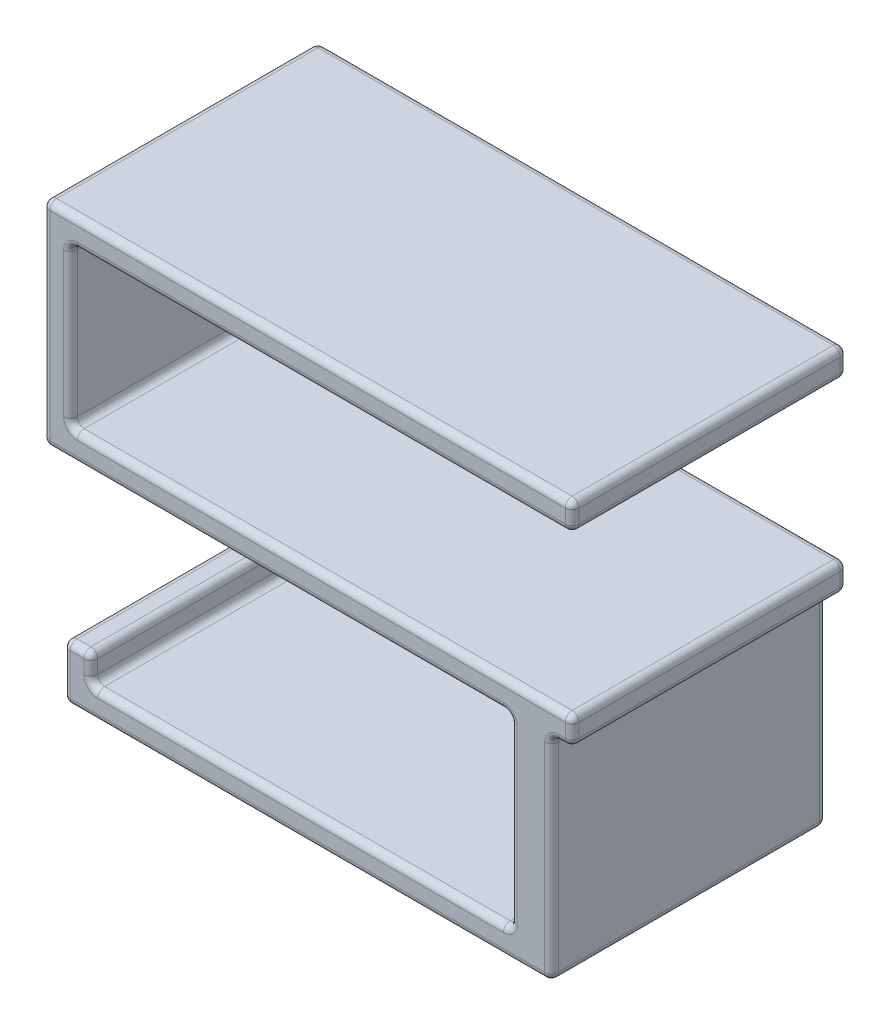
SolidWorks part; units mm, degrees
ref_plane "Plano frontal" through (0, 0, 0) normal (0, 0, 1) x (1, 0, 0)
ref_plane "Plano superior" through (0, 0, 0) normal (0, 1, 0) x (1, 0, 0)
ref_plane "Plano direito" through (0, 0, 0) normal (1, 0, 0) x (0, 0, -1)
sketch "Esboço2" plane through (0, 0, 0) normal (0, 0, 1) x (1, 0, 0)
  line L1 (-48.4735, 6.7694) -> (11.5265, 6.7694)
  line L2 (-48.4735, 6.7694) -> (-48.4735, 3.7694)
  line L3 (-48.4735, 3.7694) -> (11.5265, 3.7694)
  line L4 (11.5265, 6.7694) -> (11.5265, 3.7694)
  dimension "D1" = 3
  dimension "D2" = 60
extrude "Ressalto-extrusão2" add sketch "Esboço2" along normal blind 40
sketch "Esboço3" plane through (0, 6.7694, 0) normal (0, 1, 0) x (1, 0, 0)
  line L0 (11.5265, -40) -> (-48.4735, -40) construction
  line L1 (-46.4735, -40) -> (-62.4735, -40)
  line L2 (-46.4735, -40) -> (-46.4735, 0)
  line L3 (-46.4735, 0) -> (-62.4735, 0)
  line L4 (-62.4735, -40) -> (-62.4735, 0)
  dimension "D1" = 2
  dimension "D2" = 14
  dimension "D3" = 40
other "Alinhar grupo1"
extrude "Ressalto-extrusão3" add sketch "Esboço3" along normal blind 3
sketch "Esboço4" plane through (0, 6.7694, 0) normal (0, -1, 0) x (1, 0, 0)
  line L1 (-62.4735, 40) -> (-64.4735, 40)
  line L2 (-62.4735, 40) -> (-62.4735, 0)
  line L3 (-62.4735, 0) -> (-64.4735, 0)
  line L4 (-64.4735, 40) -> (-64.4735, 0)
  dimension "D1" = 2
  dimension "D2" = 40
extrude "Ressalto-extrusão4" add sketch "Esboço4" against normal blind 3
sketch "Esboço5" plane through (0, 6.7694, 0) normal (0, -1, 0) x (1, 0, 0)
  line L0 (-48.4735, 0) -> (-64.4735, 0) construction
  line L1 (-64.4735, 40) -> (-62.4732, 40)
  line L2 (-64.4735, 40) -> (-64.4735, 0)
  line L3 (-64.4735, 0) -> (-62.4732, 0)
  line L4 (-62.4732, 40) -> (-62.4732, 0)
  dimension "D1" = 2.0003
  dimension "D2" = 40
extrude "Ressalto-extrusão5" add sketch "Esboço5" along normal blind 26
sketch "Esboço6" plane through (0, 0, 40) normal (0, 0, 1) x (1, 0, 0)
  line L1 (-64.4735, -19.2306) -> (-46.4735, -19.2306)
  line L2 (-64.4735, -19.2306) -> (-64.4735, -16.2306)
  line L3 (-64.4735, -16.2306) -> (-46.4735, -16.2306)
  line L4 (-46.4735, -19.2306) -> (-46.4735, -16.2306)
  dimension "D1" = 18
  dimension "D2" = 3
extrude "Ressalto-extrusão6" add sketch "Esboço6" against normal blind 40
sketch "Esboço9" plane through (0, -16.2306, 0) normal (0, 1, 0) x (1, 0, 0)
  line L1 (-46.4735, -40) -> (-49.4735, -40)
  line L2 (-46.4735, -40) -> (-46.4735, 0)
  line L3 (-46.4735, 0) -> (-49.4735, 0)
  line L4 (-49.4735, -40) -> (-49.4735, 0)
  dimension "D1" = 3
  dimension "D2" = 40
extrude "Ressalto-extrusão8" add sketch "Esboço9" along normal blind 3
sketch "Esboço10" plane through (-46.4735, 0, 0) normal (1, 0, 0) x (0, 0, -1)
  line L1 (-40, -13.2306) -> (0, -13.2306)
  line L2 (-40, -13.2306) -> (-40, -16.2306)
  line L3 (-40, -16.2306) -> (0, -16.2306)
  line L4 (0, -13.2306) -> (0, -16.2306)
  dimension "D1" = 3
  dimension "D2" = 40
extrude "Ressalto-extrusão9" add sketch "Esboço10" along normal blind 60
sketch "Esboço11" plane through (0, 0, 40) normal (0, 0, 1) x (1, 0, 0)
  line L2 (-49.4735, -13.2306) -> (-48.4735, -13.2306)
  line L3 (-49.4735, -13.2306) -> (-49.4735, -16.2306)
  line L4 (-49.4735, -16.2306) -> (-48.4735, -16.2306)
  line L5 (-48.4735, -13.2306) -> (-48.4735, -16.2306)
  dimension "D1" = 3
  dimension "D2" = 1
extrude "Corte-extrusão1" cut sketch "Esboço11" against normal up to surface (40 mm away) up to face at (-36.5985, -4.7306, 0)
sketch "Esboço12" plane through (0, 0, 40) normal (0, 0, 1) x (1, 0, 0)
  line L0 (-48.4735, -13.2306) -> (13.5265, -13.2306) construction
  line L1 (13.5265, -16.2306) -> (11.5265, -16.2306)
  line L2 (13.5265, -16.2306) -> (13.5265, -13.2306)
  line L3 (13.5265, -13.2306) -> (11.5265, -13.2306)
  line L4 (11.5265, -16.2306) -> (11.5265, -13.2306)
  dimension "D1" = 3
  dimension "D2" = 2
extrude "Corte-extrusão2" cut sketch "Esboço12" against normal up to surface (40 mm away) up to face at (-36.4735, -4.7306, 0)
sketch "Esboço13" plane through (0, -16.2306, 0) normal (0, -1, 0) x (1, 0, 0)
  line L0 (11.5265, 40) -> (-46.4735, 40) construction
  line L1 (8.5265, 40) -> (5.5265, 40)
  line L2 (8.5265, 40) -> (8.5265, 0)
  line L3 (8.5265, 0) -> (5.5265, 0)
  line L4 (5.5265, 40) -> (5.5265, 0)
  line L5 (11.5265, 0) -> (-46.4735, 0) construction
  dimension "D1" = 3
  dimension "D2" = 3
  dimension "D3" = 40
extrude "Ressalto-extrusão10" add sketch "Esboço13" along normal blind 35
sketch "Esboço14" plane through (5.5265, 0, 0) normal (-1, 0, 0) x (0, 0, 1)
  line L0 (40, -51.2306) -> (40, -16.2306) construction
  line L1 (0, -51.2306) -> (40, -51.2306)
  line L2 (0, -51.2306) -> (0, -48.2306)
  line L3 (0, -48.2306) -> (40, -48.2306)
  line L4 (40, -51.2306) -> (40, -48.2306)
  dimension "D1" = 3
  dimension "D2" = 40
extrude "Ressalto-extrusão11" add sketch "Esboço14" along normal blind 60
sketch "Esboço15" plane through (0, -48.2306, 0) normal (0, 1, 0) x (1, 0, 0)
  line L1 (-54.4735, -40) -> (-52.4735, -40)
  line L2 (-54.4735, -40) -> (-54.4735, 0)
  line L3 (-54.4735, 0) -> (-52.4735, 0)
  line L4 (-52.4735, -40) -> (-52.4735, 0)
  dimension "D1" = 40
  dimension "D2" = 2
extrude "Ressalto-extrusão12" add sketch "Esboço15" along normal blind 3
sketch "Esboço16" plane through (0, -48.2306, 0) normal (0, 1, 0) x (1, 0, 0)
  line L0 (-52.4735, -40) -> (5.5265, -40) construction
  line L1 (2.5265, -40) -> (5.5265, -40)
  line L2 (2.5265, -40) -> (2.5265, 0)
  line L3 (2.5265, 0) -> (5.5265, 0)
  line L4 (5.5265, -40) -> (5.5265, 0)
  dimension "D1" = 55
  dimension "D2" = 3
  dimension "D3" = 40
extrude "Ressalto-extrusão13" add sketch "Esboço16" along normal up to surface (32 mm away) up to face at (-20.4735, -16.2306, 20)
sketch "Esboço17" plane through (-46.4735, 0, 0) normal (1, 0, 0) x (0, 0, -1)
  line L1 (-40, -19.2306) -> (0, -19.2306)
  line L2 (-40, -19.2306) -> (-40, -16.2306)
  line L3 (-40, -16.2306) -> (0, -16.2306)
  line L4 (0, -19.2306) -> (0, -16.2306)
  dimension "D1" = 40
extrude "Ressalto-extrusão14" add sketch "Esboço17" along normal blind 1
sketch "Esboço18" plane through (0, 0, 40) normal (0, 0, 1) x (1, 0, 0)
  line L1 (8.5265, -51.2306) -> (5.5265, -51.2306)
  line L2 (8.5265, -51.2306) -> (8.5265, -16.2306)
  line L3 (8.5265, -16.2306) -> (5.5265, -16.2306)
  line L4 (5.5265, -51.2306) -> (5.5265, -16.2306)
  dimension "D1" = 3
  dimension "D2" = 35
extrude "Corte-extrusão3" cut sketch "Esboço18" against normal up to surface (40 mm away) up to face at (-32.3902, -16.5639, 0)
sketch "Esboço19" plane through (0, 0, 40) normal (0, 0, 1) x (1, 0, 0)
  line L0 (11.5265, 6.7694) -> (-46.4735, 6.7694) construction
  line L1 (-46.4735, 9.7694) -> (-45.4735, 9.7694)
  line L2 (-46.4735, 9.7694) -> (-46.4735, 6.7694)
  line L3 (-46.4735, 6.7694) -> (-45.4735, 6.7694)
  line L4 (-45.4735, 9.7694) -> (-45.4735, 6.7694)
  dimension "D1" = 1
extrude "Ressalto-extrusão15" add sketch "Esboço19" against normal blind 40
sketch "Esboço20" plane through (0, 0, 40) normal (0, 0, 1) x (1, 0, 0)
  line L1 (-52.4735, -48.2306) -> (-51.4735, -48.2306)
  line L2 (-52.4735, -48.2306) -> (-52.4735, -45.2306)
  line L3 (-52.4735, -45.2306) -> (-51.4735, -45.2306)
  line L4 (-51.4735, -48.2306) -> (-51.4735, -45.2306)
  dimension "D1" = 3
  dimension "D2" = 1
extrude "Ressalto-extrusão16" add sketch "Esboço20" against normal blind 40
sketch "Esboço21" plane through (0, 0, 40) normal (0, 0, 1) x (1, 0, 0)
  line L1 (-64.4735, -19.2306) -> (-65.4735, -19.2306)
  line L2 (-64.4735, -19.2306) -> (-64.4735, 9.7694)
  line L3 (-64.4735, 9.7694) -> (-65.4735, 9.7694)
  line L4 (-65.4735, -19.2306) -> (-65.4735, 9.7694)
  dimension "D1" = 1
  dimension "D2" = 29
extrude "Ressalto-extrusão17" add sketch "Esboço21" against normal up to surface (40 mm away) up to face at (-32.4735, -16.5639, 0)
sketch "Esboço22" plane through (0, 0, 40) normal (0, 0, 1) x (1, 0, 0)
  line L2 (-45.4735, -19.2306) -> (11.5265, -19.2306)
  line L3 (-45.4735, -19.2306) -> (-45.4735, -16.2306)
  line L4 (-45.4735, -16.2306) -> (11.5265, -16.2306)
  line L5 (11.5265, -19.2306) -> (11.5265, -16.2306)
extrude "Ressalto-extrusão18" add sketch "Esboço22" against normal up to surface (40 mm away) up to face at (-32.5568, -16.5639, 0)
sketch "Esboço23" plane through (0, 0, 40) normal (0, 0, 1) x (1, 0, 0)
  line L0 (11.5265, -13.2306) -> (11.5265, -19.2306) construction
  line L1 (-48.4735, -13.2306) -> (11.5265, -13.2306)
  line L2 (-48.4735, -13.2306) -> (-48.4735, -16.2306)
  line L3 (-48.4735, -16.2306) -> (11.5265, -16.2306)
  line L4 (11.5265, -13.2306) -> (11.5265, -16.2306)
  dimension "D1" = 3
  dimension "D2" = 60
extrude "Corte-extrusão4" cut sketch "Esboço23" against normal up to surface (40 mm away) up to face at (-31.3826, -16.8669, 0)
sketch "Esboço24" plane through (0, 0, 40) normal (0, 0, 1) x (1, 0, 0)
  line L3 (11.5265, -19.2306) -> (-65.4735, -19.2306)
  line L4 (11.5265, -19.2306) -> (11.5265, -20.2306)
  line L5 (11.5265, -20.2306) -> (-65.4735, -20.2306)
  line L6 (-65.4735, -19.2306) -> (-65.4735, -20.2306)
  dimension "D1" = 77
  dimension "D2" = 1
extrude "Ressalto-extrusão19" add sketch "Esboço24" against normal up to surface (40 mm away) up to face at (-29.6735, -17.2306, 0)
sketch "Esboço25" plane through (0, 0, 40) normal (0, 0, 1) x (1, 0, 0)
  line L1 (11.5265, 6.7694) -> (-65.4735, 6.7694)
  line L2 (11.5265, 6.7694) -> (11.5265, 10.7694)
  line L3 (11.5265, 10.7694) -> (-65.4735, 10.7694)
  line L4 (-65.4735, 6.7694) -> (-65.4735, 10.7694)
  dimension "D1" = 77
  dimension "D2" = 4
extrude "Ressalto-extrusão20" add sketch "Esboço25" against normal up to surface (40 mm away) up to face at (-29.6735, -17.4306, 0)
sketch "Esboço26" plane through (0, 0, 40) normal (0, 0, 1) x (1, 0, 0)
  line L0 (11.5265, 3.7694) -> (11.5265, 10.7694) construction
  line L1 (-48.4735, 3.7694) -> (11.5265, 3.7694)
  line L2 (-48.4735, 3.7694) -> (-48.4735, 6.7694)
  line L3 (-48.4735, 6.7694) -> (11.5265, 6.7694)
  line L4 (11.5265, 3.7694) -> (11.5265, 6.7694)
  dimension "D1" = 3
  dimension "D2" = 60
extrude "Corte-extrusão5" cut sketch "Esboço26" against normal up to surface (40 mm away) up to face at (-27.9179, -20.0084, 0)
sketch "Esboço27" plane through (0, 0, 40) normal (0, 0, 1) x (1, 0, 0)
  line L0 (-62.4732, 6.7694) -> (11.5265, 6.7694) construction
  line L1 (-62.4732, -16.2306) -> (-61.4732, -16.2306)
  line L2 (-62.4732, -16.2306) -> (-62.4732, 6.7694)
  line L3 (-62.4732, 6.7694) -> (-61.4732, 6.7694)
  line L4 (-61.4732, -16.2306) -> (-61.4732, 6.7694)
  dimension "D1" = 1
extrude "Ressalto-extrusão21" add sketch "Esboço27" against normal up to surface (40 mm away) up to face at (-25.3485, -22.9806, 0)
sketch "Esboço28" plane through (0, 0, 40) normal (0, 0, 1) x (1, 0, 0)
  line L0 (5.5265, -20.2306) -> (11.5265, -20.2306) construction
  line L1 (5.5265, -51.2306) -> (8.5265, -51.2306)
  line L2 (5.5265, -51.2306) -> (5.5265, -20.2306)
  line L3 (5.5265, -20.2306) -> (8.5265, -20.2306)
  line L4 (8.5265, -51.2306) -> (8.5265, -20.2306)
  dimension "D1" = 3
extrude "Ressalto-extrusão22" add sketch "Esboço28" against normal up to surface (40 mm away) up to face at (-25.2235, -22.9806, 0)
sketch "Esboço29" plane through (0, 0, 40) normal (0, 0, 1) x (1, 0, 0)
  line L0 (-51.4735, -48.2306) -> (-51.4735, -45.2306) construction
  line L1 (2.5265, -48.2306) -> (-51.4735, -48.2306)
  line L2 (2.5265, -48.2306) -> (2.5265, -47.2306)
  line L3 (2.5265, -47.2306) -> (-51.4735, -47.2306)
  line L4 (-51.4735, -48.2306) -> (-51.4735, -47.2306)
  dimension "D1" = 54
  dimension "D2" = 1
extrude "Ressalto-extrusão24" add sketch "Esboço29" against normal up to surface (40 mm away) up to face at (-24.8485, -22.9806, 0)
sketch "Esboço33" plane through (0, 0, 40) normal (0, 0, 1) x (1, 0, 0)
  line L0 (8.5265, -51.2306) -> (-54.4735, -51.2306) construction
  line L1 (-51.5065, -51.2306) -> (-55.5065, -51.2306)
  line L2 (-51.5065, -51.2306) -> (-51.5065, -43.2306)
  line L3 (-51.5065, -43.2306) -> (-55.5065, -43.2306)
  line L4 (-55.5065, -51.2306) -> (-55.5065, -43.2306)
  dimension "D1" = 4
  dimension "D2" = 8
extrude "Ressalto-extrusão25" add sketch "Esboço33" against normal up to surface (40 mm away) up to face at (-24.8485, -22.8556, 0)
sketch "Esboço35" plane through (0, 0, 40) normal (0, 0, 1) x (1, 0, 0)
  line L1 (-51.4735, -47.2306) -> (-55.5065, -47.2306)
  line L2 (-51.4735, -47.2306) -> (-51.4735, -43.2306)
  line L3 (-51.4735, -43.2306) -> (-55.5065, -43.2306)
  line L4 (-55.5065, -47.2306) -> (-55.5065, -43.2306)
extrude "Corte-extrusão6" cut sketch "Esboço35" against normal up to surface (40 mm away) up to face at (-27.9253, -25.1195, 0)
sketch "Esboço36" plane through (0, 0, 40) normal (0, 0, 1) x (1, 0, 0)
  line L1 (-55.5065, -51.2306) -> (-58.5065, -51.2306)
  line L2 (-55.5065, -51.2306) -> (-55.5065, -47.2306)
  line L3 (-55.5065, -47.2306) -> (-58.5065, -47.2306)
  line L4 (-58.5065, -51.2306) -> (-58.5065, -47.2306)
  dimension "D1" = 4
  dimension "D2" = 3
extrude "Ressalto-extrusão26" add sketch "Esboço36" against normal up to surface (40 mm away) up to face at (-21.1925, -19.6592, 0)
sketch "Esboço37" plane through (0, 0, 40) normal (0, 0, 1) x (1, 0, 0)
  line L1 (-58.5065, -51.2306) -> (-62.5065, -51.2306)
  line L2 (-58.5065, -51.2306) -> (-58.5065, -43.2306)
  line L3 (-58.5065, -43.2306) -> (-62.5065, -43.2306)
  line L4 (-62.5065, -51.2306) -> (-62.5065, -43.2306)
  dimension "D1" = 8
  dimension "D2" = 4
extrude "Ressalto-extrusão27" add sketch "Esboço37" against normal up to surface (40 mm away) up to face at (-21.6211, -19.6592, 0)
fillet "Filete1" radius 1 16 edges at (-65.4735, 10.7694, 20) (-61.4732, 6.7694, 20) (-61.4732, -16.2306, 20) (-65.4735, -20.2306, 20) (2.5265, -20.2306, 20) (2.5265, -47.2306, 20) (-58.5065, -47.2306, 20) (-58.5065, -43.2306, 20) (-62.5065, -51.2306, 20) (-62.5065, -43.2306, 20) (8.5265, -51.2306, 20) (8.5265, -20.2306, 20) (11.5265, -20.2306, 20) (11.5265, -16.2306, 20) (11.5265, 10.7694, 20) (11.5265, 6.7694, 20)
fillet "Filete2" radius 1 64 edges at (-58.2136, -46.9377, 0) (-58.2136, -46.9377, 40) (-58.5065, -45.2306, 40) (-58.5065, -45.2306, 0) (-58.7994, -43.5235, 0) (-58.7994, -43.5235, 40) (-60.5065, -43.2306, 40) (-60.5065, -43.2306, 0) (-62.2136, -43.5235, 0) (-62.2136, -43.5235, 40) (-62.5065, -47.2306, 0) (-62.5065, -47.2306, 40) (-62.2136, -50.9377, 0) (-62.2136, -50.9377, 40) (-26.99, -51.2306, 0) (8.2336, -50.9377, 0) (8.2336, -50.9377, 40) (8.5265, -35.7306, 40) (8.5265, -35.7306, 0) (8.8194, -20.5235, 0) (8.8194, -20.5235, 40) (10.0265, -20.2306, 40) (10.0265, -20.2306, 0) (11.2336, -19.9377, 0) (11.2336, -19.9377, 40) (11.5265, -18.2306, 40) (11.5265, -18.2306, 0) (11.2336, -16.5235, 0) (11.2336, -16.5235, 40) (-24.9734, -16.2306, 0) (-24.9734, -16.2306, 40) (-61.1803, -15.9377, 0) (-61.1803, -15.9377, 40) (-61.4732, -4.7306, 0) (-61.4732, -4.7306, 40) (-61.1803, 6.4765, 0) (-61.1803, 6.4765, 40) (-24.9734, 6.7694, 0) (11.2336, 7.0623, 0) (11.2336, 7.0623, 40) (11.5265, 8.7694, 0) (11.5265, 8.7694, 40) (11.2336, 10.4765, 0) (11.2336, 10.4765, 40) (-26.9735, 10.7694, 0) (-26.9735, 10.7694, 40) (-65.1806, 10.4765, 0) (-65.1806, 10.4765, 40) (-65.4735, -4.7306, 40) (-65.4735, -4.7306, 0) (-65.1806, -19.9377, 0) (-65.1806, -19.9377, 40) (-31.4735, -20.2306, 40) (-31.4735, -20.2306, 0) (2.2336, -20.5235, 40) (2.2336, -20.5235, 0) (2.5265, -33.7306, 0) (2.2336, -46.9377, 0) (2.2336, -46.9377, 40) (2.5265, -33.7306, 40) (-24.9734, 6.7694, 40) (-26.99, -51.2306, 40) (-27.99, -47.2306, 40) (-27.99, -47.2306, 0)
